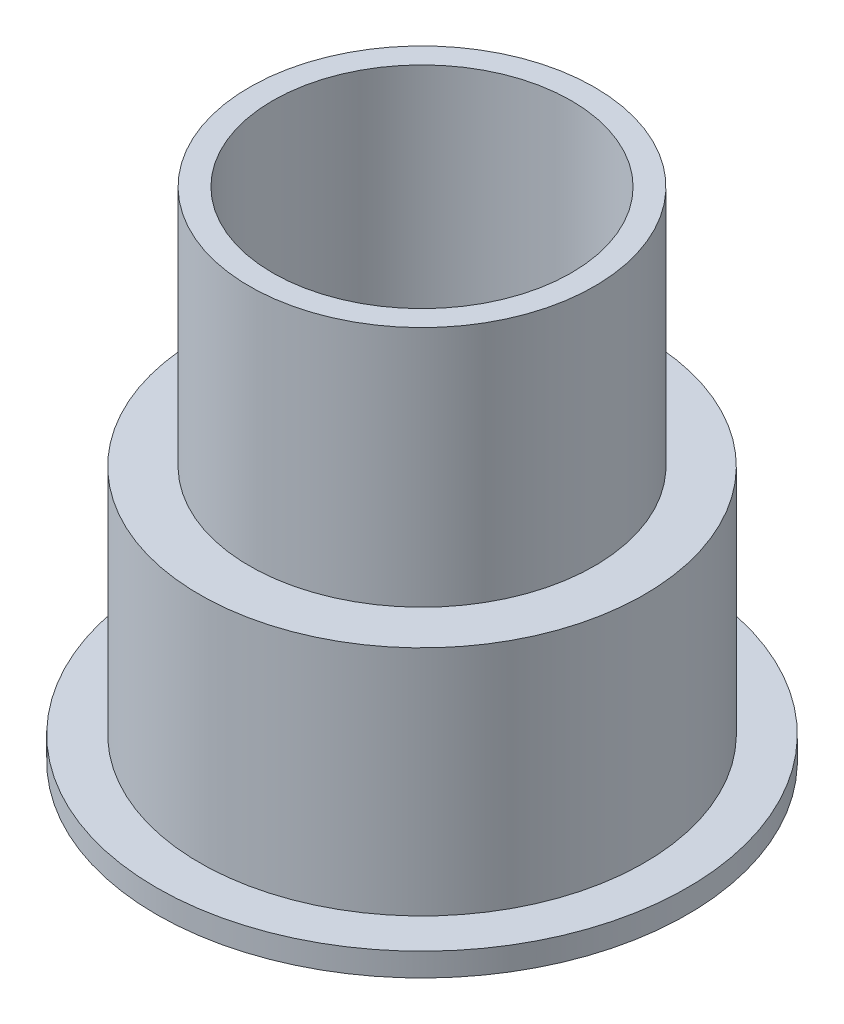
SolidWorks part; units mm, degrees
ref_plane "Front Plane" through (0, 0, 0) normal (0, 0, 1) x (1, 0, 0)
ref_plane "Top Plane" through (0, 0, 0) normal (0, 1, 0) x (1, 0, 0)
ref_plane "Right Plane" through (0, 0, 0) normal (1, 0, 0) x (0, 0, -1)
sketch "Sketch1" plane through (0, 0, 0) normal (0, 0, 1) x (1, 0, 0)
  line L0 (0, 0) -> (0, 13.5207) construction
  line L1 (6, -0.8548) -> (6, 6.1452)
  line L2 (6, 6.1452) -> (0, 6.1452)
  line L3 (4.5, 6.8452) -> (4.5, 14.1452)
  line L4 (6, -0.8548) -> (8, -0.8548)
  line L5 (5.2, 6.8452) -> (5.2, 14.1452)
  line L6 (6.7, -0.1548) -> (8, -0.1548)
  line L7 (6.7, -0.1548) -> (6.7, 6.8452)
  line L8 (6.7, 6.8452) -> (5.2, 6.8452)
  line L9 (0, 6.8452) -> (0, 6.1452)
  line L10 (4.5, 14.1452) -> (5.2, 14.1452)
  line L11 (8, -0.8548) -> (8, -0.1548)
  line L12 (4.5, 6.1452) -> (4.5, 14.1452) construction
  line L13 (4.5, 6.8452) -> (0, 6.8452)
  line L14 (6.7, 6.8452) -> (0, 6.8452) construction
  line L15 (5.2, 6.1452) -> (5.2, 14.1452) construction
  dimension "D1" = 6
  dimension "D2" = 2
  dimension "D3" = 7
  dimension "D5" = 1.5
  dimension "D6" = 0.7
  dimension "D7" = 0.7
revolve "Revolve1" add sketch "Sketch1" angle 360 about L0
